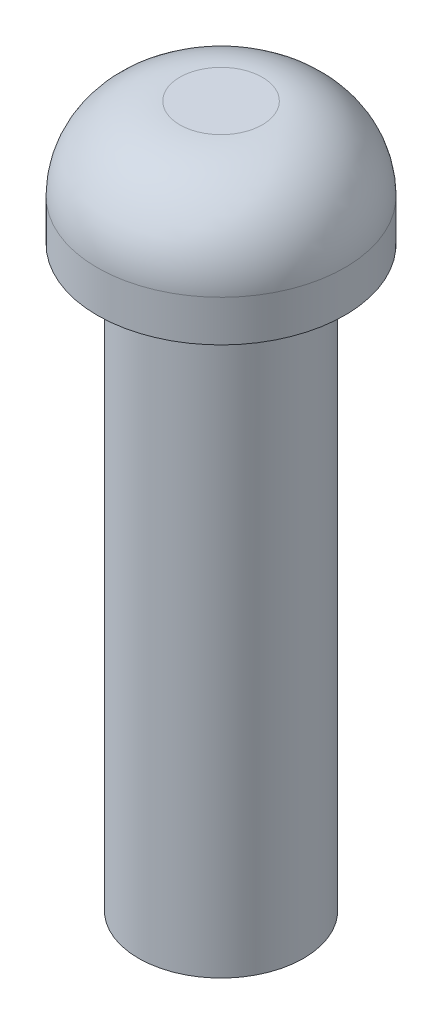
SolidWorks part; units mm, degrees
ref_plane "Plan de face" through (0, 0, 0) normal (0, 0, 1) x (1, 0, 0)
ref_plane "Plan de dessus" through (0, 0, 0) normal (0, 1, 0) x (1, 0, 0)
ref_plane "Plan de droite" through (0, 0, 0) normal (1, 0, 0) x (0, 0, -1)
sketch "Esquisse1" plane through (0, 0, 0) normal (0, 1, 0) x (1, 0, 0)
  circle A0 centre (0, 0) radius 15
extrude "Boss.-Extru.1" add sketch "Esquisse1" along normal blind 15
fillet "Congé1" radius 10 1 edges at (0, 15, 15)
sketch "Esquisse3" plane through (0, 0, 0) normal (0, -1, 0) x (1, 0, 0)
  circle A0 centre (0, 0) radius 10
extrude "Boss.-Extru.3" add sketch "Esquisse3" along normal blind 70
